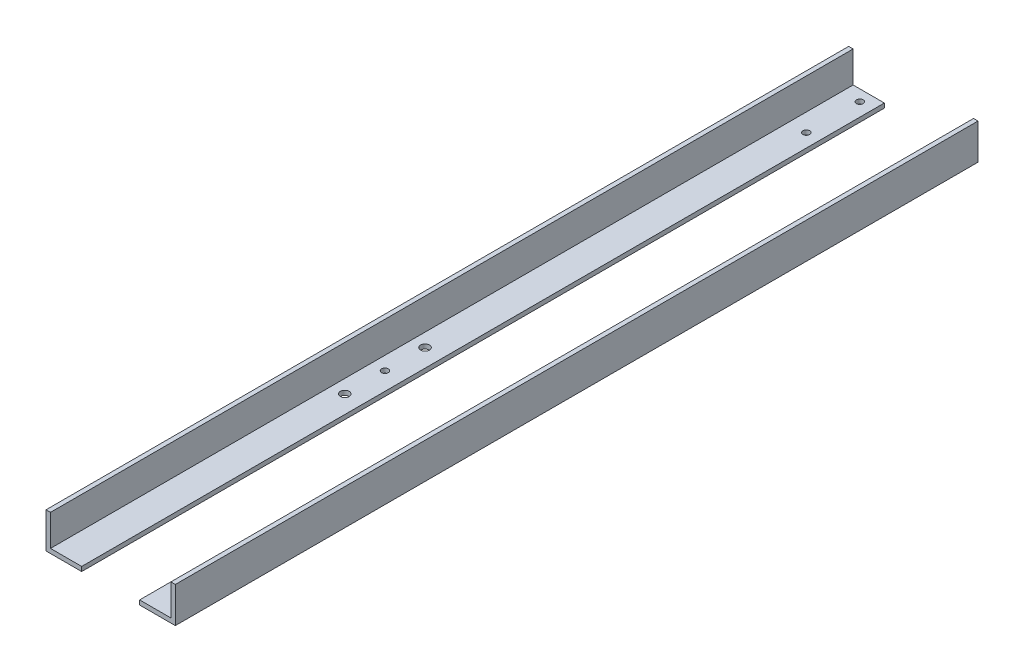
SolidWorks part; units mm, degrees
ref_plane "Front Plane" through (0, 0, 0) normal (0, 0, 1) x (1, 0, 0)
ref_plane "Top Plane" through (0, 0, 0) normal (0, 1, 0) x (1, 0, 0)
ref_plane "Right Plane" through (0, 0, 0) normal (1, 0, 0) x (0, 0, -1)
sketch "Sketch1" plane through (0, 0, 0) normal (0, 1, 0) x (1, 0, 0)
  line L1 (-92.075, -571.5) -> (92.075, -571.5)
  line L2 (-92.075, -571.5) -> (-92.075, 571.5)
  line L3 (-92.075, 571.5) -> (92.075, 571.5)
  line L4 (92.075, -571.5) -> (92.075, 571.5)
  line L5 (-92.075, -571.5) -> (92.075, 571.5) construction
  line L6 (-92.075, 571.5) -> (92.075, -571.5) construction
  point P0 (0, 0)
  dimension "D1" = 1143
  dimension "D2" = 184.15
extrude "Boss-Extrude1" add sketch "Sketch1" along normal blind 50.8
sketch "Sketch2" plane through (0, 0, 571.5) normal (0, 0, 1) x (1, 0, 0)
  line L0 (-92.075, 50.8) -> (92.075, 50.8) construction
  line L1 (-85.725, 50.8) -> (85.725, 50.8)
  line L2 (-85.725, 50.8) -> (-85.725, 6.35)
  line L3 (-85.725, 6.35) -> (-41.275, 6.35)
  line L4 (85.725, 50.8) -> (85.725, 6.35)
  line L5 (-92.075, 50.8) -> (-92.075, 0) construction
  line L6 (92.075, 50.8) -> (92.075, 0) construction
  line L7 (-92.075, 0) -> (92.075, 0) construction
  line L9 (-41.275, 6.35) -> (-41.275, 0)
  line L10 (-41.275, 0) -> (41.275, 0)
  line L11 (41.275, 6.35) -> (41.275, 0)
  line L12 (41.275, 6.35) -> (85.725, 6.35)
  point P16 (-41.275, 3.175)
  dimension "D1" = 6.35
  dimension "D2" = 6.35
  dimension "D3" = 44.45
  dimension "D4" = 50.8
  dimension "D5" = 50.8
extrude "Cut-Extrude1" cut sketch "Sketch2" against normal through all
sketch "Sketch3" plane through (0, 6.35, 0) normal (0, 1, 0) x (1, 0, 0)
  line L0 (-85.725, 571.5) -> (-41.275, 571.5) construction
  line L2 (-41.275, 571.5) -> (-41.275, -571.5) construction
  line L3 (-85.725, -571.5) -> (-41.275, -571.5) construction
  line L4 (41.275, 571.5) -> (41.275, -571.5) construction
  circle A0 centre (-60.325, 555.625) radius 4.7625
  circle A1 centre (-60.325, 479.425) radius 4.7625
  circle A2 centre (-66.675, -114.3) radius 4.7625
  circle A3 centre (60.325, 555.625) radius 4.7625
  circle A4 centre (60.325, 479.425) radius 4.7625
  circle A6 centre (60.325, -114.3) radius 4.7625
  circle A7 centre (-66.675, -57.15) radius 6.35
  circle A8 centre (-66.675, -171.45) radius 6.35
  circle A9 centre (60.325, -57.15) radius 6.35
  circle A10 centre (60.325, -171.45) radius 6.35
  point P28 (0, 0)
  point P29 (0, 0)
  point P30 (0, 0)
  dimension "D6" = 9.525
  dimension "D7" = 9.525
  dimension "D8" = 9.525
  dimension "D10" = 9.525
  dimension "D11" = 9.525
  dimension "D12" = 9.525
  dimension "D13" = 12.7
  dimension "D14" = 12.7
  dimension "D17" = 12.7
  dimension "D18" = 12.7
  dimension "D1" = 15.875
  dimension "D2" = 19.05
  dimension "D3" = 92.075
  dimension "D4" = 25.4
  dimension "D5" = 457.2
  dimension "D9" = 19.05
  dimension "D15" = 57.15
  dimension "D16" = 57.15
  dimension "D19" = 57.15
  dimension "D20" = 0
  dimension "D21" = 57.15
extrude "Bolt Hole Cuts" cut sketch "Sketch3" against normal through all
